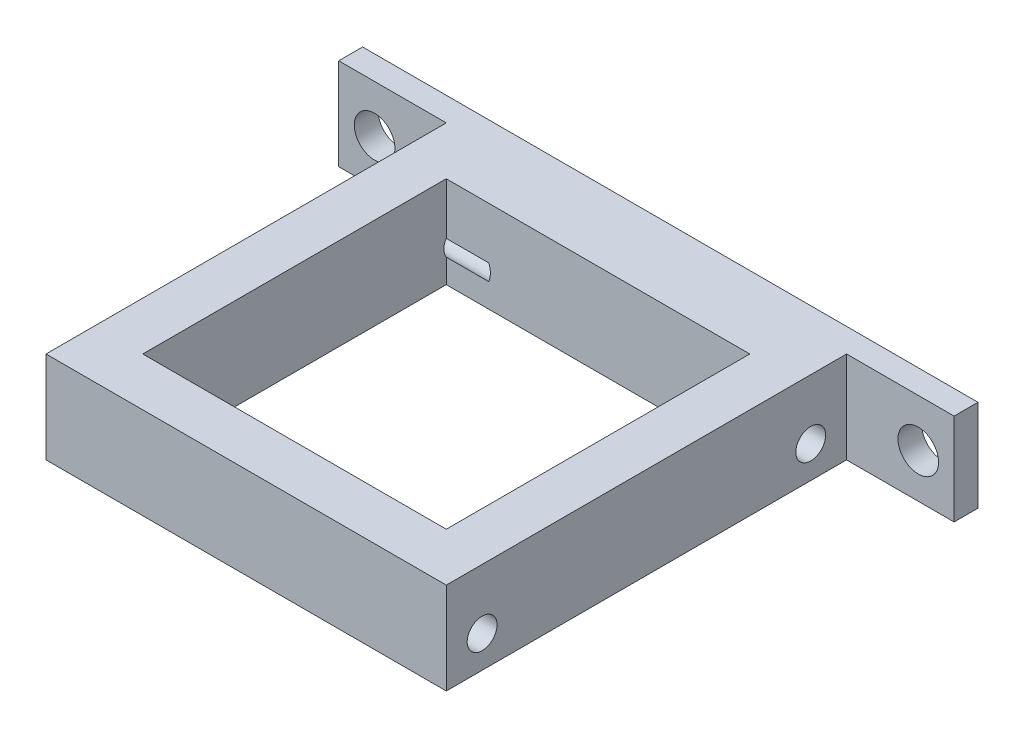
SolidWorks part; units mm, degrees
ref_plane "Front Plane" through (0, 0, 0) normal (0, 0, 1) x (1, 0, 0)
ref_plane "Top Plane" through (0, 0, 0) normal (0, 1, 0) x (1, 0, 0)
ref_plane "Right Plane" through (0, 0, 0) normal (1, 0, 0) x (0, 0, -1)
sketch "Sketch1" plane through (0, 0, 0) normal (0, 1, 0) x (1, 0, 0)
  line L1 (-16.75, 16.75) -> (16.75, 16.75)
  line L2 (-16.75, 16.75) -> (-16.75, -16.75)
  line L3 (-16.75, -16.75) -> (16.75, -16.75)
  line L4 (16.75, 16.75) -> (16.75, -16.75)
  line L5 (-16.75, 16.75) -> (16.75, -16.75) construction
  line L6 (-16.75, -16.75) -> (16.75, 16.75) construction
  point P0 (0, 0)
  dimension "D1" = 33.5
  dimension "D2" = 33.5
extrude "Boss-Extrude1" add sketch "Sketch1" along normal blind 70
hole_wizard "M3x0.5 Tapped Hole1" positions "3DSketch3" profile "Sketch5" tap size "M3x0.5" standard "ANSI Metric"
sketch3d "3DSketch3"
  line L0 (-16.75, 70, -16.75) -> (-16.75, 70, 16.75) construction
  line L1 (-16.75, 70, 16.75) -> (16.75, 70, 16.75) construction
  line L2 (16.75, 70, -16.75) -> (-16.75, 70, -16.75) construction
  line L3 (16.75, 70, 16.75) -> (16.75, 70, -16.75) construction
  point P0 (13.75, 70, 13.75)
  point P2 (-13.75, 70, -13.75)
  dimension "D1" = 30.5
  dimension "D2" = 3
  dimension "D3" = 3
  dimension "D4" = 30.5
sketch "Sketch5" plane through (13.75, 70, 13.75) normal (1, 0, 0) x (0, 0, 1)
  line L0 (0, 0) -> (0, 8.3711)
  line L1 (0, 8.3711) -> (1.25, 7.62)
  line L2 (1.25, 7.62) -> (1.25, 0)
  line L5 (1.25, 0) -> (0, 0)
  line L10 (0, 8.3711) -> (-1.25, 7.62) construction
  line L11 (0, -6.35) -> (0, 107.95) construction
  dimension "Tap Drill Dia." = 2.5
  dimension "Tap Drill Depth" = 7.62
  dimension "Drill Angle" = 118
hole_wizard "M3x0.5 Tapped Hole2" positions "3DSketch4" profile "Sketch6" tap size "M3x0.5" standard "ANSI Metric"
sketch3d "3DSketch4"
  line L0 (16.75, 70, 16.75) -> (16.75, 0, 16.75) construction
  line L1 (16.75, 70, -16.75) -> (16.75, 0, -16.75) construction
  line L2 (16.75, 0, 16.75) -> (16.75, 0, -16.75) construction
  point P0 (16.75, 6, 13.75)
  point P2 (16.75, 6, -13.75)
  dimension "D1" = 3
  dimension "D2" = 3
  dimension "D3" = 6
  dimension "D4" = 6
sketch "Sketch6" plane through (16.75, 6, 13.75) normal (0, 1, 0) x (0, 0, -1)
  line L0 (0, 0) -> (0, 8.3711)
  line L1 (0, 8.3711) -> (1.25, 7.62)
  line L2 (1.25, 7.62) -> (1.25, 0)
  line L5 (1.25, 0) -> (0, 0)
  line L10 (0, 8.3711) -> (-1.25, 7.62) construction
  line L11 (0, -6.35) -> (0, 107.95) construction
  dimension "Tap Drill Dia." = 2.5
  dimension "Tap Drill Depth" = 7.62
  dimension "Drill Angle" = 118
sketch "Sketch7" plane through (0, 0, -16.75) normal (0, 0, -1) x (-1, 0, 0)
  line L0 (-16.75, 70) -> (-16.75, 0) construction
  line L1 (-16.75, 11) -> (-22.75, 11)
  line L2 (-16.75, 11) -> (-16.75, 61)
  line L3 (-16.75, 61) -> (-22.75, 61)
  line L4 (-22.75, 11) -> (-22.75, 61)
  line L5 (-16.75, 0) -> (16.75, 0) construction
  dimension "D1" = 6
  dimension "D2" = 11
  dimension "D3" = 50
extrude "Boss-Extrude2" add sketch "Sketch7" against normal blind 3 separate body
sketch "Sketch8" plane through (0, 0, -16.75) normal (0, 0, -1) x (-1, 0, 0)
  line L0 (16.75, 70) -> (16.75, 0) construction
  line L1 (16.75, 61) -> (22.75, 61)
  line L2 (16.75, 61) -> (16.75, 11)
  line L3 (16.75, 11) -> (22.75, 11)
  line L4 (22.75, 61) -> (22.75, 11)
  line L5 (-22.75, 11) -> (-16.75, 11) construction
  line L7 (16.75, 0) -> (-16.75, 0) construction
  dimension "D1" = 6
  dimension "D2" = 0
  dimension "D3" = 50
  dimension "D4" = 11
extrude "Boss-Extrude3" add sketch "Sketch8" against normal blind 3 separate body
hole_wizard "M3 Clearance Hole1" positions "3DSketch5" profile "Sketch10" hole size "M3" standard "ANSI Metric" end condition through all
sketch3d "3DSketch5"
  line L0 (22.75, 11, -16.75) -> (16.75, 11, -16.75) construction
  line L1 (22.75, 61, -16.75) -> (22.75, 11, -16.75) construction
  line L2 (-22.75, 11, -16.75) -> (-22.75, 61, -16.75) construction
  point P0 (19.75, 51, -16.75)
  point P2 (19.75, 26, -16.75)
  point P4 (-19.75, 51, -16.75)
  point P6 (-19.75, 26, -16.75)
  dimension "D1" = 40
  dimension "D2" = 15
  dimension "D3" = 3
  dimension "D4" = 3
  dimension "D5" = 3
  dimension "D6" = 3
  dimension "D7" = 40
  dimension "D8" = 15
sketch "Sketch10" plane through (19.75, 51, -16.75) normal (1, 0, 0) x (0, 1, 0)
  line L0 (0, 0) -> (0, 33.5)
  line L1 (0, 33.5) -> (1.7, 33.5)
  line L2 (1.7, 33.5) -> (1.7, 0)
  line L5 (1.7, 0) -> (0, 0)
  line L11 (0, -6.35) -> (0, 107.95) construction
  dimension "Thru Hole Dia." = 3.4
  dimension "Thru Hole Depth" = 33.5
sketch "Sketch12" plane through (0, 0, 16.75) normal (0, 0, 1) x (1, 0, 0)
  line L0 (16.75, 70) -> (16.75, 0) construction
  line L1 (16.75, 13) -> (-16.75, 13)
  line L2 (16.75, 13) -> (16.75, 58)
  line L3 (16.75, 58) -> (-16.75, 58)
  line L4 (-16.75, 13) -> (-16.75, 58)
  line L5 (-16.75, 70) -> (-16.75, 0) construction
  line L6 (-16.75, 0) -> (16.75, 0) construction
  line L7 (-16.75, 70) -> (16.75, 70) construction
  dimension "D1" = 13
  dimension "D2" = 12
extrude "Cut-Extrude2" cut sketch "Sketch12" against normal blind 32.5
hole_wizard "M3x0.5 Tapped Hole3" positions "Sketch15" profile "Sketch13" tap size "M3x0.5" standard "ANSI Metric"
sketch "Sketch15" plane through (-16.75, 0, 0) normal (-1, 0, 0) x (0, 0, 1)
  line L0 (-16.75, 70) -> (-16.75, 0) construction
  line L1 (-16.75, 0) -> (16.75, 0) construction
  line L2 (16.75, 13) -> (16.75, 0) construction
  point P0 (-13.75, 6)
  point P2 (13.75, 6)
  dimension "D1" = 3
  dimension "D2" = 6
  dimension "D3" = 3
  dimension "D4" = 6
sketch "Sketch13" plane through (-16.75, 6, -13.75) normal (0, 1, 0) x (0, 0, 1)
  line L0 (0, 0) -> (0, 8.3711)
  line L1 (0, 8.3711) -> (1.25, 7.62)
  line L2 (1.25, 7.62) -> (1.25, 0)
  line L5 (1.25, 0) -> (0, 0)
  line L10 (0, 8.3711) -> (-1.25, 7.62) construction
  line L11 (0, -6.35) -> (0, 107.95) construction
  dimension "Tap Drill Dia." = 2.5
  dimension "Tap Drill Depth" = 7.62
  dimension "Drill Angle" = 118
sketch "Sketch16" plane through (0, 0, 16.75) normal (0, 0, 1) x (1, 0, 0)
  line L1 (-22.75, 11) -> (22.75, 11)
  line L2 (-22.75, 11) -> (-22.75, 70.86)
  line L3 (-22.75, 70.86) -> (22.75, 70.86)
  line L4 (22.75, 11) -> (22.75, 70.86)
extrude "Cut-Extrude3" cut sketch "Sketch16" against normal through all
sketch "Sketch17" plane through (0, 0, -16.75) normal (0, 0, -1) x (-1, 0, 0)
  line L0 (-16.75, 11) -> (-16.75, 0) construction
  line L1 (25.75, 0) -> (-25.75, 0)
  line L2 (25.75, 0) -> (25.75, 11)
  line L3 (25.75, 11) -> (-25.75, 11)
  line L4 (-25.75, 0) -> (-25.75, 11)
  line L5 (16.75, 11) -> (16.75, 0) construction
  dimension "D1" = 9
  dimension "D2" = 9
extrude "Boss-Extrude4" add sketch "Sketch17" along normal blind 2
sketch "Sketch22" plane through (0, 0, -18.75) normal (0, 0, -1) x (-1, 0, 0)
  line L0 (25.75, 0) -> (25.75, 11) construction
  line L1 (-25.75, 0) -> (25.75, 0)
  line L2 (-25.75, 0) -> (-25.75, 3.3229)
  line L3 (-25.75, 3.3229) -> (25.75, 3.3229)
  line L4 (25.75, 0) -> (25.75, 3.3229)
extrude "Cut-Extrude5" cut sketch "Sketch22" against normal through all
hole_wizard "M3 Clearance Hole3" positions "3DSketch7" profile "Sketch23" hole size "M3" standard "ANSI Metric" end condition through all
sketch3d "3DSketch7"
  line L0 (-25.75, 3.3229, -16.75) -> (-25.75, 11, -16.75) construction
  line L1 (25.75, 11, -16.75) -> (25.75, 3.3229, -16.75) construction
  line L2 (16.75, 11, -16.75) -> (25.75, 11, -16.75) construction
  line L3 (-25.75, 11, -16.75) -> (-16.75, 11, -16.75) construction
  point P0 (22.75, 7, -16.75)
  point P2 (-22.75, 7, -16.75)
  dimension "D1" = 3
  dimension "D2" = 3
  dimension "D3" = 4
  dimension "D4" = 4
sketch "Sketch23" plane through (22.75, 7, -16.75) normal (1, 0, 0) x (0, -1, 0)
  line L0 (0, 0) -> (0, 2)
  line L1 (0, 2) -> (1.7, 2)
  line L2 (1.7, 2) -> (1.7, 0)
  line L5 (1.7, 0) -> (0, 0)
  line L11 (0, -6.35) -> (0, 107.95) construction
  dimension "Thru Hole Dia." = 3.4
  dimension "Thru Hole Depth" = 2
sketch "Sketch24" plane through (0, 11, 0) normal (0, 1, 0) x (1, 0, 0)
  line L0 (-16.75, -16.75) -> (16.75, -16.75) construction
  line L1 (12.7, -12.7) -> (-12.7, -12.7)
  line L2 (12.7, -12.7) -> (12.7, 12.7)
  line L3 (12.7, 12.7) -> (-12.7, 12.7)
  line L4 (-12.7, -12.7) -> (-12.7, 12.7)
  line L5 (16.75, 16.75) -> (16.75, -16.75) construction
  dimension "D1" = 4.05
  dimension "D2" = 25.4
  dimension "D3" = 4.05
  dimension "D4" = 25.4
extrude "Cut-Extrude6" cut sketch "Sketch24" against normal through all
